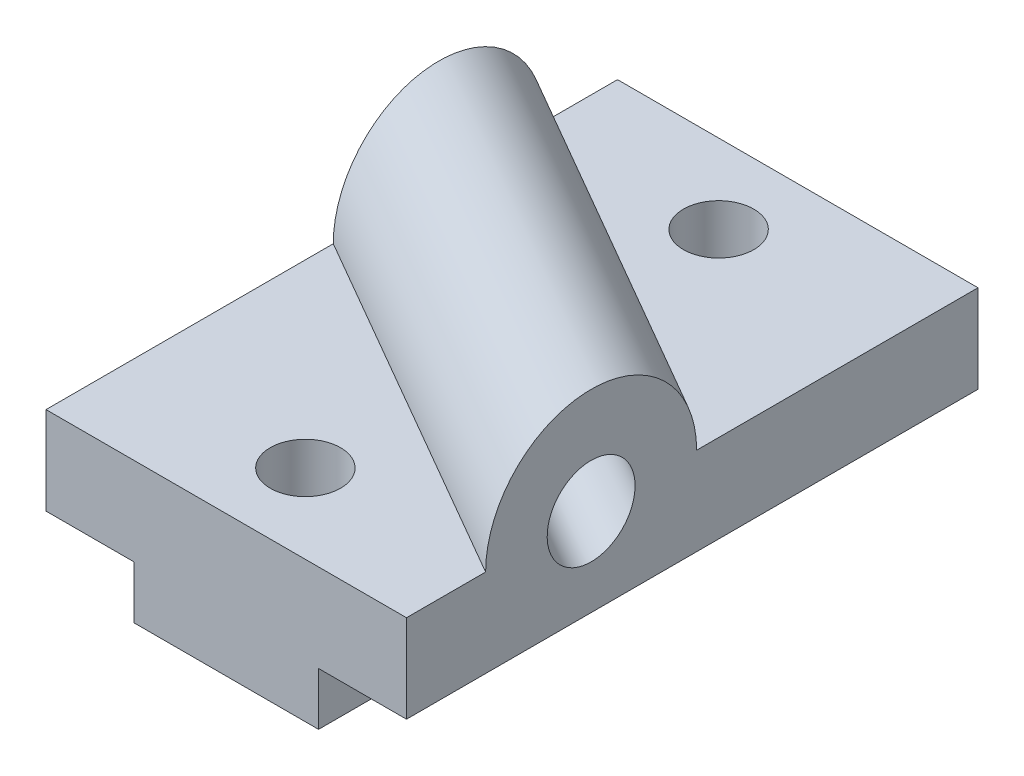
SolidWorks part; units mm, degrees
ref_plane "Front Plane" through (0, 0, 0) normal (0, 0, 1) x (1, 0, 0)
ref_plane "Top Plane" through (0, 0, 0) normal (0, 1, 0) x (1, 0, 0)
ref_plane "Right Plane" through (0, 0, 0) normal (1, 0, 0) x (0, 0, -1)
sketch "Sketch2" plane through (0, 0, 0) normal (0, 0, 1) x (1, 0, 0)
  line L0 (0, 9.525) -> (-15.875, 9.525)
  line L1 (0, 0) -> (33.3375, 0)
  line L2 (0, 0) -> (0, 9.525)
  line L4 (33.3375, 0) -> (33.3375, 9.525)
  line L5 (-15.875, 9.525) -> (-15.875, 25.4)
  line L6 (-15.875, 25.4) -> (49.2125, 25.4)
  line L7 (49.2125, 25.4) -> (49.2125, 9.525)
  line L8 (49.2125, 9.525) -> (33.3375, 9.525)
  dimension "D1" = 15.875
  dimension "D2" = 9.525
  dimension "D3" = 25.4
  dimension "D4" = 65.0875
extrude "Boss-Extrude1" add sketch "Sketch2" along normal mid plane 103.1875
sketch "Sketch3" plane through (49.2125, 0, 0) normal (1, 0, 0) x (0, 0, -1)
  line L2 (-51.5938, 25.4) -> (51.5938, 25.4) construction
  line L4 (0.7937, 25.4) -> (-37.3062, 25.4)
  line L5 (-51.5938, 9.525) -> (-51.5938, 25.4) construction
  arc A0 (-37.3062, 25.4) -> (0.7937, 25.4) centre (-18.2563, 25.4) cw
  point P8 (-18.2563, 25.4)
  dimension "D1" = 19.05
  dimension "D2" = 33.3375
sketch "Sketch4" plane through (0, 25.4, 0) normal (0, 1, 0) x (1, 0, 0)
  line L0 (49.2125, -18.2563) -> (-15.875, 19.322)
  line L5 (-15.875, -51.5938) -> (-15.875, 51.5938) construction
  line L6 (49.2125, -51.5938) -> (49.2125, 51.5938) construction
  dimension "D1" = 60
extrude "Boss-Extrude2" add sketch "Sketch3" along direction (-0.866, 0, -0.5) on the side against the normal up to surface (65.0875 mm away) contours A0 L4
sketch "Sketch5" plane through (49.2125, 0, 0) normal (1, 0, 0) x (0, 0, -1)
  line L0 (-18.2563, 25.4) -> (19.322, 25.4) construction
  circle A0 centre (-18.2563, 25.4) radius 7.9375
  dimension "D1" = 15.875
extrude "Cut-Extrude1" cut sketch "Sketch5" along direction (-0.866, 0, -0.5) on the side against the normal through all
sketch "Sketch6" plane through (0, 25.4, 0) normal (0, 1, 0) x (1, 0, 0)
  line L0 (16.6687, 51.5938) -> (16.6688, -51.5938) construction
  line L1 (49.2125, 51.5938) -> (-15.875, 51.5938) construction
  line L2 (49.2125, -51.5938) -> (-15.875, -51.5938) construction
  line L3 (49.2125, 0.7937) -> (49.2125, 51.5938) construction
  circle A0 centre (16.6688, -37.3063) radius 6.35
  circle A1 centre (16.6687, 37.3062) radius 6.35
  dimension "D1" = 12.7
  dimension "D2" = 14.2875
  dimension "D3" = 14.2875
  dimension "D4" = 32.5437
extrude "Cut-Extrude2" cut sketch "Sketch6" against normal through all
